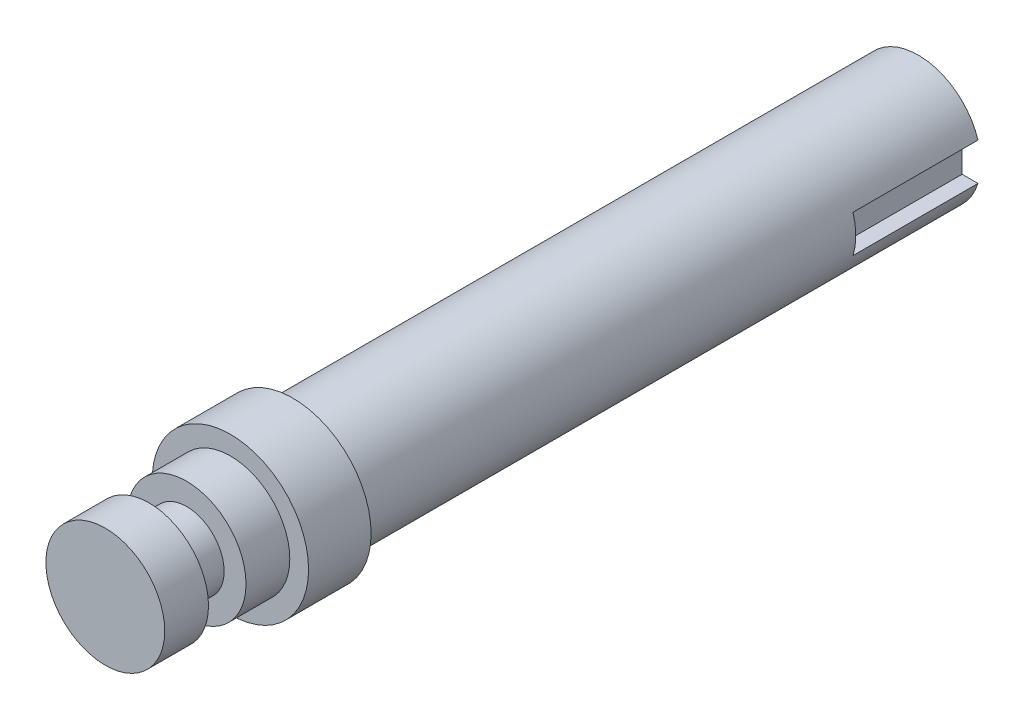
SolidWorks part; units mm, degrees
ref_plane "Front" through (0, 0, 0) normal (0, 0, 1) x (1, 0, 0)
ref_plane "Top" through (0, 0, 0) normal (0, 1, 0) x (1, 0, 0)
ref_plane "Right" through (0, 0, 0) normal (1, 0, 0) x (0, 0, -1)
sketch "Sketch1" plane through (0, 0, 0) normal (0, 0, 1) x (1, 0, 0)
  circle A0 centre (0, 0) radius 10
  dimension "D1" = 20
extrude "Boss-Extrude1" add sketch "Sketch1" along normal blind 100 contours A0
sketch "Sketch2" plane through (0, 0, 100) normal (0, 0, 1) x (1, 0, 0)
  circle A0 centre (0, 0) radius 12.5
  dimension "D1" = 25
extrude "Boss-Extrude2" add sketch "Sketch2" along normal blind 10
sketch "Sketch3" plane through (0, 0, 110) normal (0, 0, 1) x (1, 0, 0)
  circle A0 centre (0, 0) radius 9.5
  dimension "D1" = 19
extrude "Boss-Extrude3" add sketch "Sketch3" along normal blind 7
sketch "Sketch4" plane through (0, 0, 117) normal (0, 0, 1) x (1, 0, 0)
  circle A0 centre (0, 0) radius 6
  dimension "D1" = 12
extrude "Boss-Extrude4" add sketch "Sketch4" along normal blind 6
sketch "Sketch5" plane through (0, 0, 123) normal (0, 0, 1) x (1, 0, 0)
  circle A0 centre (0, 0) radius 9.5
  dimension "D1" = 19
extrude "Boss-Extrude5" add sketch "Sketch5" along normal blind 7
sketch "Sketch6" plane through (0, 0, 0) normal (0, 0, -1) x (-1, 0, 0)
  line L0 (-7, -3) -> (-12, -3)
  line L1 (-7, 0) -> (-12, 0)
  line L2 (-7, -3) -> (-7, 3)
  line L3 (-7, 3) -> (-12, 3)
  line L4 (-12, -3) -> (-12, 3)
  dimension "D1" = 3
  dimension "D2" = 7
  dimension "D3" = 5
  dimension "D4" = 5
  dimension "D5" = 3
extrude "Cut-Extrude1" cut sketch "Sketch6" against normal blind 20 contours L3 L4 L0 L2
